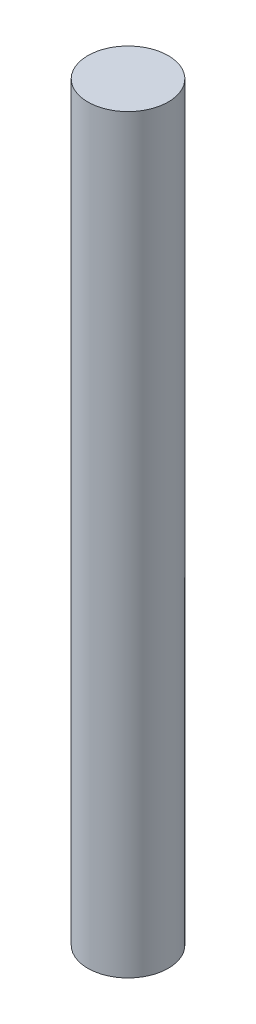
SolidWorks part; units mm, degrees
ref_plane "Front Plane" through (0, 0, 0) normal (0, 0, 1) x (1, 0, 0)
ref_plane "Top Plane" through (0, 0, 0) normal (0, 1, 0) x (1, 0, 0)
ref_plane "Right Plane" through (0, 0, 0) normal (1, 0, 0) x (0, 0, -1)
sketch "Sketch1" plane through (0, 0, 0) normal (1, 0, 0) x (0, 0, -1)
  line L0 (0, 0) -> (0, 140)
  line L1 (0, 140) -> (7.5, 140)
  line L2 (7.5, 140) -> (7.5, 0)
  line L3 (7.5, 0) -> (0, 0)
  dimension "D1" = 140
  dimension "D2" = 7.5
revolve "Revolve1" add sketch "Sketch1" angle 360 about L0
